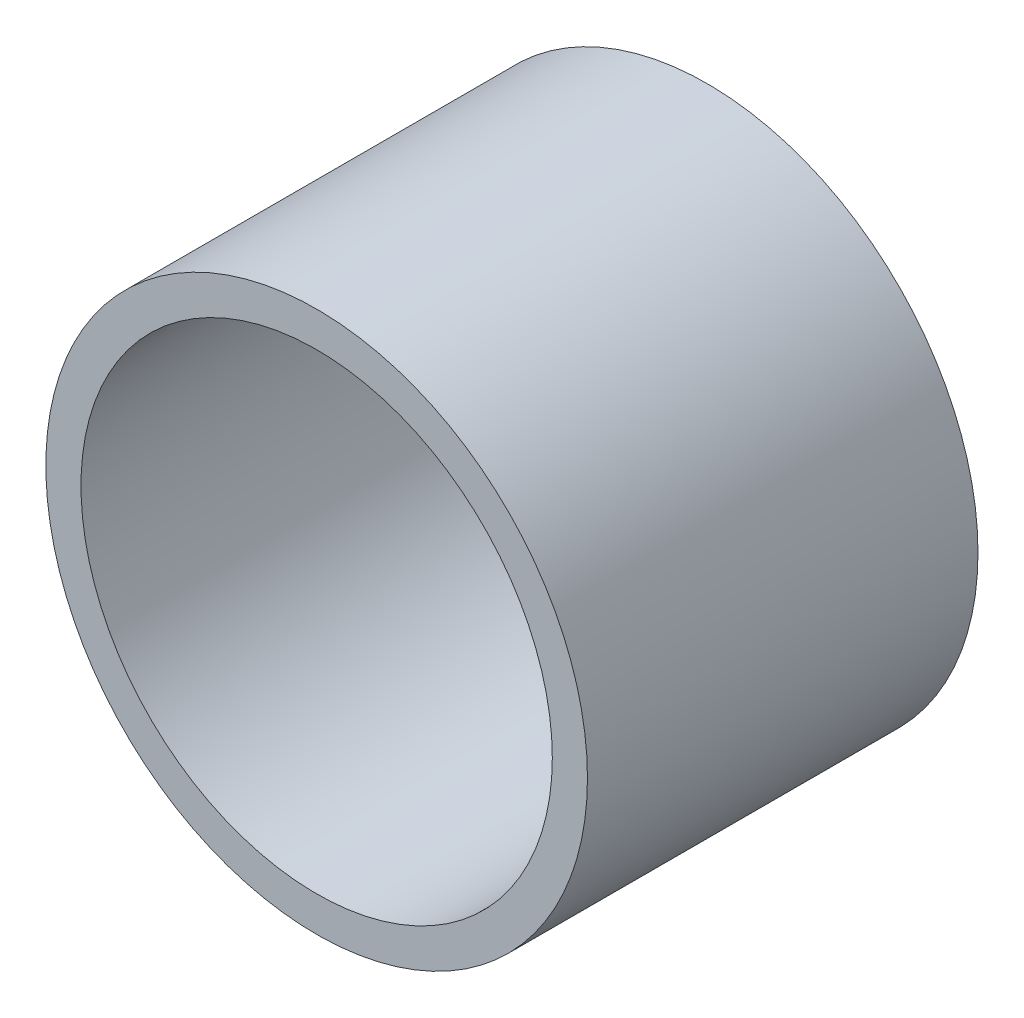
SolidWorks part; units mm, degrees
ref_plane "Alzado" through (0, 0, 0) normal (0, 0, 1) x (1, 0, 0)
ref_plane "Planta" through (0, 0, 0) normal (0, 1, 0) x (1, 0, 0)
ref_plane "Vista lateral" through (0, 0, 0) normal (1, 0, 0) x (0, 0, -1)
sketch "Croquis1" plane through (0, 0, 0) normal (0, 0, 1) x (1, 0, 0)
  circle A0 centre (0, 0) radius 30.165
  circle A1 centre (0, 0) radius 26.25
  dimension "D1" = 52.5
  dimension "D2" = 60.33
extrude "Saliente-Extruir1" add sketch "Croquis1" along normal blind 43.5
